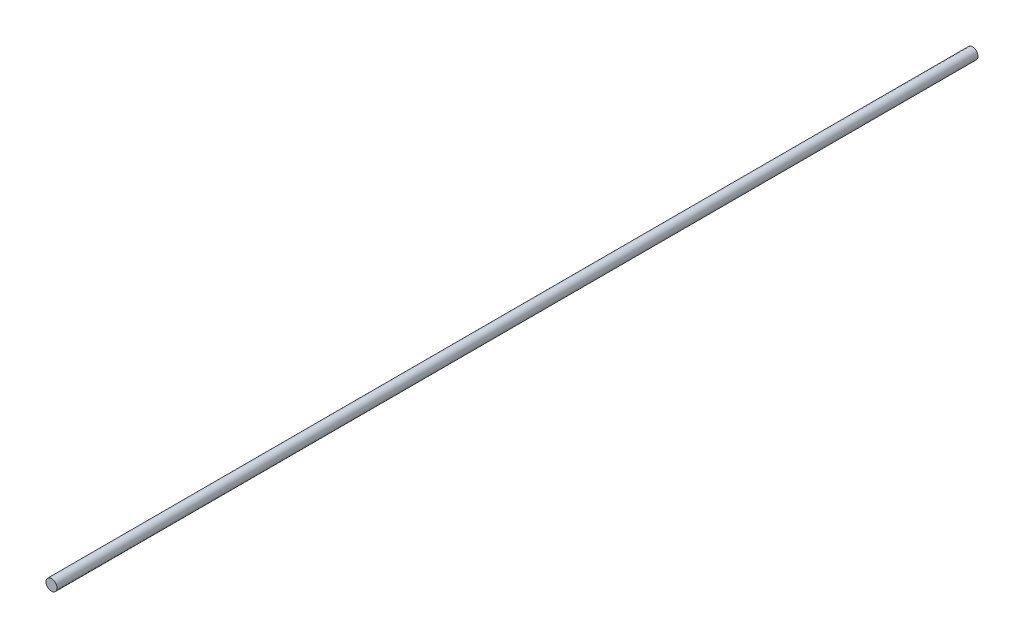
SolidWorks part; units mm, degrees
ref_plane "Front Plane" through (0, 0, 0) normal (0, 0, 1) x (1, 0, 0)
ref_plane "Top Plane" through (0, 0, 0) normal (0, 1, 0) x (1, 0, 0)
ref_plane "Right Plane" through (0, 0, 0) normal (1, 0, 0) x (0, 0, -1)
sketch "Sketch1" plane through (0, 0, 0) normal (0, 0, 1) x (1, 0, 0)
  circle A0 centre (0, 0) radius 3.175
  dimension "D1" = 6.35
extrude "Boss-Extrude1" add sketch "Sketch1" along normal blind 532.435
